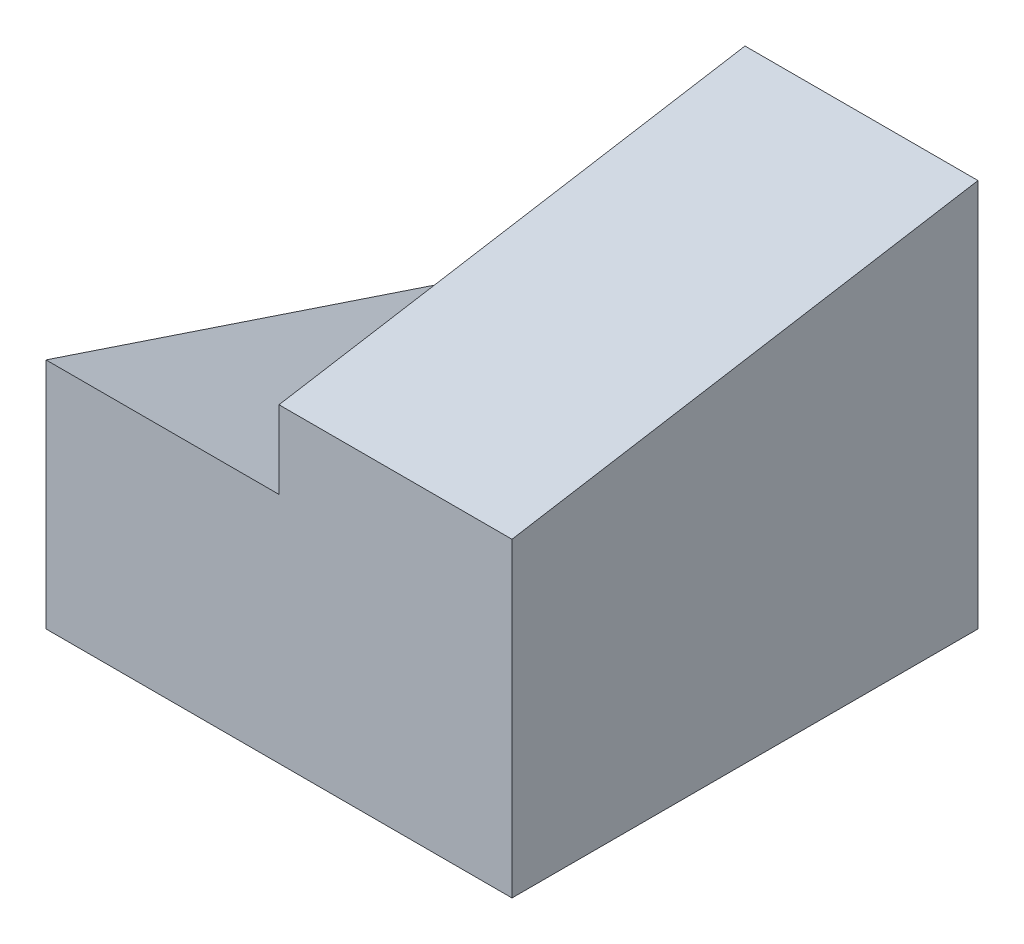
SolidWorks part; units mm, degrees
ref_plane "Front Plane" through (0, 0, 0) normal (0, 0, 1) x (1, 0, 0)
ref_plane "Top Plane" through (0, 0, 0) normal (0, 1, 0) x (1, 0, 0)
ref_plane "Right Plane" through (0, 0, 0) normal (1, 0, 0) x (0, 0, -1)
sketch "Sketch3" plane through (0, 0, 0) normal (0, 0, 1) x (1, 0, 0)
  line L1 (0, 0) -> (6, 0)
  line L2 (0, 0) -> (0, 5)
  line L3 (0, 5) -> (6, 5)
  line L4 (6, 0) -> (6, 5)
  dimension "D1" = 5
  dimension "D2" = 6
extrude "Boss-Extrude6" add sketch "Sketch3" along normal blind 6
sketch "Sketch7" plane through (0, 0, 0) normal (-1, 0, 0) x (0, 0, 1)
  line L0 (0, 5) -> (6, 4)
  line L1 (6, 5) -> (6, 0) construction
  line L2 (6, 4) -> (6, 5)
  line L3 (6, 5) -> (0, 5)
  dimension "D1" = 1
extrude "Cut-Extrude4" cut sketch "Sketch7" against normal blind 6
sketch "Sketch8" plane through (0, 0, 0) normal (-1, 0, 0) x (0, 0, 1)
  line L0 (0, 5) -> (6, 4)
  line L1 (6, 4) -> (6, 3)
  line L2 (6, 4) -> (6, 0) construction
  line L3 (6, 3) -> (0, 1)
  line L4 (0, 5) -> (0, 0) construction
  line L5 (0, 1) -> (0, 5)
  dimension "D1" = 1
  dimension "D2" = 2
extrude "Cut-Extrude5" cut sketch "Sketch8" against normal blind 3
